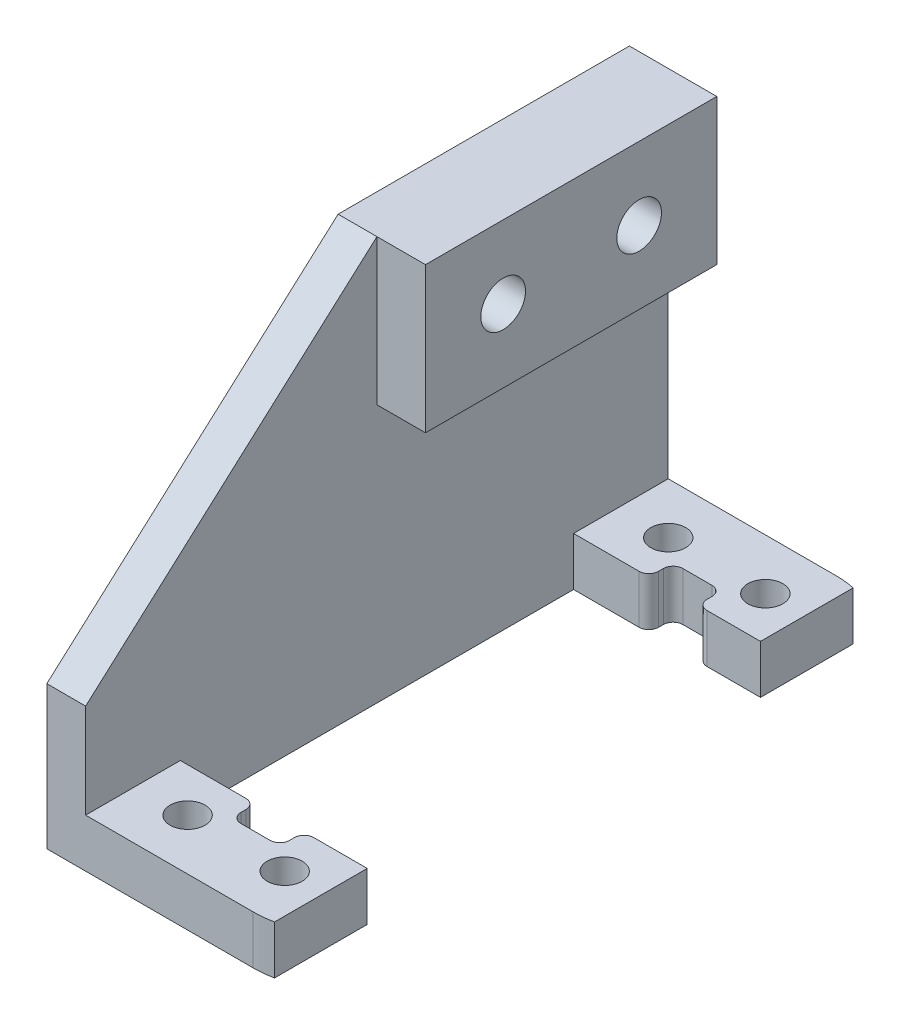
SolidWorks part; units mm, degrees
ref_plane "Front Plane" through (0, 0, 0) normal (0, 0, 1) x (1, 0, 0)
ref_plane "Top Plane" through (0, 0, 0) normal (0, 1, 0) x (1, 0, 0)
ref_plane "Right Plane" through (0, 0, 0) normal (1, 0, 0) x (0, 0, -1)
sketch "Sketch1" plane through (0, 0, 0) normal (0, 1, 0) x (1, 0, 0)
  line L1 (25, -30) -> (-25, -30)
  line L2 (25, -30) -> (25, 30)
  line L3 (25, 30) -> (-25, 30)
  line L4 (-25, -30) -> (-25, 30)
  line L5 (25, -30) -> (-25, 30) construction
  line L6 (25, 30) -> (-25, -30) construction
  point P0 (0, 0)
  dimension "D1" = 50
  dimension "D2" = 60
extrude "Boss-Extrude1" add sketch "Sketch1" along normal blind 5
sketch "Sketch2" plane through (0, 5, 0) normal (0, 1, 0) x (1, 0, 0)
  line L1 (18.25, -20.25) -> (-2.25, -20.25)
  line L2 (18.25, -20.25) -> (18.25, 20.25)
  line L3 (18.25, 20.25) -> (-2.25, 20.25)
  line L4 (-2.25, -20.25) -> (-2.25, 20.25)
  line L5 (18.25, -20.25) -> (-2.25, 20.25) construction
  line L6 (18.25, 20.25) -> (-2.25, -20.25) construction
  point P0 (8, 0)
  dimension "D1" = 20.5
  dimension "D2" = 40.5
  dimension "D3" = 0
  dimension "D4" = 8
extrude "Cut-Extrude1" cut sketch "Sketch2" against normal blind 5
sketch "Sketch3" plane through (0, 5, 0) normal (0, 1, 0) x (1, 0, 0)
  line L0 (8, 20.25) -> (8, -20.25) construction
  line L1 (18.25, 20.25) -> (-2.25, 20.25) construction
  line L2 (-2.25, -20.25) -> (18.25, -20.25) construction
  line L3 (-55, 0) -> (55, 0) construction
  circle A0 centre (3, 24.75) radius 1.8
  circle A1 centre (13, 24.75) radius 1.8
  circle A2 centre (13, -24.75) radius 1.8
  circle A3 centre (3, -24.75) radius 1.8
  dimension "D1" = 5
  dimension "D2" = 10
  dimension "D3" = 24.75
extrude "Cut-Extrude2" cut sketch "Sketch3" against normal blind 5
sketch "Sketch4" plane through (0, 5, 0) normal (0, 1, 0) x (1, 0, 0)
  line L0 (25, 30) -> (-25, 30) construction
  line L1 (-25, 30) -> (-25, -30) construction
  line L2 (-25, -30) -> (25, -30) construction
  circle A0 centre (-17.5, 20) radius 2.5
  circle A1 centre (-17.5, -20) radius 2.5
  dimension "D1" = 10
  dimension "D2" = 7.5
  dimension "D3" = 10
  dimension "D4" = 7.5
extrude "Cut-Extrude3" cut sketch "Sketch4" against normal blind 5
fillet "Fillet1" radius 10 4 edges at (25, 2.5, 30) (-25, 2.5, 30) (-25, 2.5, -30) (25, 2.5, -30)
sketch "Sketch5" plane through (0, 5, 0) normal (0, 1, 0) x (1, 0, 0)
  line L0 (18.25, 20.25) -> (-2.25, 20.25) construction
  line L1 (10.5, 17.75) -> (5.5, 17.75)
  line L2 (10.5, 17.75) -> (10.5, 22.75)
  line L3 (10.5, 22.75) -> (5.5, 22.75)
  line L4 (5.5, 17.75) -> (5.5, 22.75)
  line L5 (10.5, 17.75) -> (5.5, 22.75) construction
  line L6 (10.5, 22.75) -> (5.5, 17.75) construction
  point P0 (8, 20.25)
  dimension "D1" = 5
  dimension "D2" = 5
extrude "Cut-Extrude4" cut sketch "Sketch5" against normal blind 10
mirror "Mirror1" about plane through (0, 0, 0) normal (0, 0, 1) of "Cut-Extrude4"
fillet "Fillet2" radius 1 8 edges at (5.5, 2.5, 20.25) (10.5, 2.5, 20.25) (10.5, 2.5, 22.75) (5.5, 2.5, 22.75) (10.5, 2.5, -20.25) (10.5, 2.5, -22.75) (5.5, 2.5, -22.75) (5.5, 2.5, -20.25)
sketch "Sketch6" plane through (0, 5, 0) normal (0, 1, 0) x (1, 0, 0)
  line L0 (15, 30) -> (-15, 30) construction
  line L1 (17, 30) -> (34.9438, 30)
  line L2 (17, 30) -> (17, -30)
  line L3 (17, -30) -> (34.9438, -30)
  line L4 (34.9438, 30) -> (34.9438, -30)
  line L5 (25, -20) -> (25, 20) construction
  dimension "D1" = 8
extrude "Cut-Extrude5" cut sketch "Sketch6" against normal blind 10
sketch "Sketch7" plane through (0, 5, 0) normal (0, 1, 0) x (1, 0, 0)
  line L0 (-15, -30) -> (15, -30) construction
  line L1 (-2.25, -30) -> (-6.25, -30)
  line L2 (-2.25, -30) -> (-2.25, 30)
  line L3 (-2.25, 30) -> (-6.25, 30)
  line L4 (-6.25, -30) -> (-6.25, 30)
  line L5 (15, 30) -> (-15, 30) construction
  line L6 (-2.25, 20.25) -> (-2.25, -20.25) construction
  dimension "D1" = 4
  dimension "D2" = 0
extrude "Boss-Extrude2" add sketch "Sketch7" along normal blind 36.6
sketch "Sketch8" plane through (0, 5, 0) normal (0, 1, 0) x (1, 0, 0)
  line L1 (-6.25, -30) -> (-28.1149, -30)
  line L2 (-6.25, -30) -> (-6.25, 39.9489)
  line L3 (-6.25, 39.9489) -> (-28.1149, 39.9489)
  line L4 (-28.1149, -30) -> (-28.1149, 39.9489)
extrude "Cut-Extrude6" cut sketch "Sketch8" against normal blind 24
sketch "Sketch9" plane through (-2.25, 0, 0) normal (1, 0, 0) x (0, 0, -1)
  line L1 (30, 41.6) -> (0, 41.6)
  line L2 (30, 41.6) -> (30, 26.6)
  line L3 (30, 26.6) -> (0, 26.6)
  line L4 (0, 41.6) -> (0, 26.6)
  dimension "D1" = 15
  dimension "D2" = 30
extrude "Boss-Extrude3" add sketch "Sketch9" along normal blind 5
sketch "Sketch10" plane through (-2.25, 0, 0) normal (1, 0, 0) x (0, 0, -1)
  line L0 (0, 41.6) -> (-30, 14.7281)
  line L1 (-30, 41.6) -> (-30, 5) construction
  line L2 (-30, 14.7281) -> (-30, 41.6)
  line L3 (-30, 41.6) -> (0, 41.6)
extrude "Cut-Extrude7" cut sketch "Sketch10" against normal blind 5
sketch "Sketch11" plane through (2.75, 0, 0) normal (1, 0, 0) x (0, 0, -1)
  line L0 (0, 41.6) -> (0, 26.6) construction
  line L1 (30, 26.6) -> (30, 41.6) construction
  circle A0 centre (8, 34.1) radius 2.3
  circle A1 centre (22, 34.1) radius 2.3
  dimension "D1" = 4.6
  dimension "D2" = 8
  dimension "D3" = 8
extrude "Cut-Extrude8" cut sketch "Sketch11" against normal blind 13
